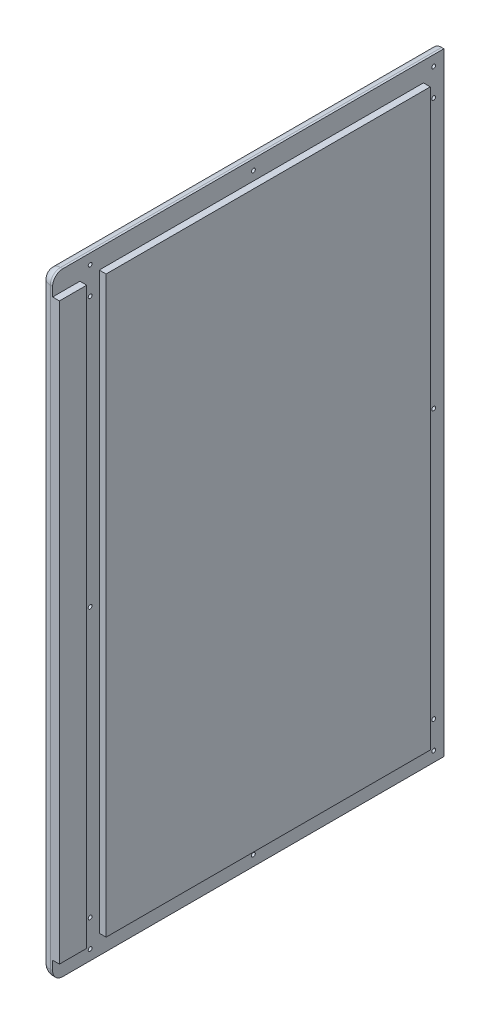
SolidWorks part; units mm, degrees
ref_plane "Front Plane" through (0, 0, 0) normal (0, 0, 1) x (1, 0, 0)
ref_plane "Top Plane" through (0, 0, 0) normal (0, 1, 0) x (1, 0, 0)
ref_plane "Right Plane" through (0, 0, 0) normal (1, 0, 0) x (0, 0, -1)
sketch "Sketch1" plane through (0, 0, 0) normal (1, 0, 0) x (0, 0, -1)
  line L1 (0, 0) -> (376.55, 0)
  line L2 (0, 0) -> (0, 570)
  line L3 (0, 570) -> (376.55, 570)
  line L4 (376.55, 0) -> (376.55, 570)
  dimension "D1" = 376.55
  dimension "D2" = 570
extrude "Boss-Extrude1" add sketch "Sketch1" along normal blind 18
sketch "Sketch5" plane through (18, 0, 0) normal (1, 0, 0) x (0, 0, -1)
  line L0 (0, 570) -> (0, 0) construction
  line L1 (56.1, 563.65) -> (38.1, 563.65)
  line L2 (56.1, 563.65) -> (56.1, 6.35)
  line L3 (56.1, 6.35) -> (38.1, 6.35)
  line L4 (38.1, 563.65) -> (38.1, 6.35)
  line L5 (0, 0) -> (376.55, 0) construction
  line L6 (376.55, 570) -> (0, 570) construction
  dimension "D1" = 18
  dimension "D2" = 38.1
  dimension "D3" = 6.35
  dimension "D4" = 6.35
extrude "Cut-Extrude3" cut sketch "Sketch5" against normal blind 6.35
sketch "Sketch6" plane through (18, 0, 0) normal (1, 0, 0) x (0, 0, -1)
  line L0 (376.55, 0) -> (376.55, 570) construction
  line L1 (376.55, 563.65) -> (363.85, 563.65)
  line L2 (376.55, 563.65) -> (376.55, 6.35)
  line L3 (376.55, 6.35) -> (363.85, 6.35)
  line L4 (363.85, 563.65) -> (363.85, 6.35)
  line L5 (0, 0) -> (376.55, 0) construction
  line L6 (376.55, 570) -> (0, 570) construction
  dimension "D1" = 12.7
  dimension "D2" = 6.35
  dimension "D3" = 6.35
sketch "Sketch7" plane through (18, 0, 0) normal (1, 0, 0) x (0, 0, -1)
  line L0 (376.55, 563.65) -> (376.55, 6.35) construction
  line L1 (0, 0) -> (376.55, 0)
  line L2 (0, 0) -> (0, 18)
  line L3 (0, 18) -> (376.55, 18)
  line L4 (376.55, 0) -> (376.55, 18)
  line L6 (0, 570) -> (376.55, 570)
  line L7 (0, 570) -> (0, 552)
  line L8 (0, 552) -> (376.55, 552)
  line L9 (376.55, 570) -> (376.55, 552)
  dimension "D1" = 18
  dimension "D2" = 18
extrude "Cut-Extrude4" cut sketch "Sketch7" against normal blind 6.35
fillet "Fillet1" radius 9.525 5 edges at (0, 0, -188.275) (0, 285, 0) (0, 570, -188.275) (5.825, 0, 0) (5.825, 570, 0)
sketch "Sketch9" plane through (18, 0, 0) normal (1, 0, 0) x (0, 0, -1)
  line L0 (56.1, 552) -> (376.55, 552) construction
  line L1 (376.55, 18) -> (357.5, 18)
  line L2 (376.55, 18) -> (376.55, 552)
  line L3 (376.55, 552) -> (357.5, 552)
  line L4 (357.5, 18) -> (357.5, 552)
  dimension "D1" = 19.05
extrude "Cut-Extrude6" cut sketch "Sketch9" against normal up to surface (6.35 mm away) up to face at (11.65, 285, -122.1218)
sketch "Sketch10" plane through (18, 0, 0) normal (1, 0, 0) x (0, 0, -1)
  line L0 (376.55, 570) -> (9.525, 570) construction
  line L1 (12.7, 570) -> (0, 570)
  line L2 (12.7, 570) -> (12.7, 0)
  line L3 (12.7, 0) -> (0, 0)
  line L4 (0, 570) -> (0, 0)
  line L5 (0, 552) -> (0, 18) construction
  line L6 (9.525, 0) -> (376.55, 0) construction
  dimension "D1" = 12.7
extrude "Cut-Extrude7" cut sketch "Sketch10" against normal through all
fillet "Fillet2" radius 9.525 5 edges at (10.5875, 570, -12.7) (2.7898, 567.2102, -12.7) (0, 285, -12.7) (10.5875, 0, -12.7) (2.7898, 2.7898, -12.7)
sketch "Sketch11" plane through (11.65, 0, 0) normal (1, 0, 0) x (0, 0, -1)
  line L0 (376.55, 285) -> (-301.8505, 285) construction
  line L1 (376.55, 0) -> (376.55, 570) construction
  line L2 (199.3875, 570) -> (199.3875, -127.0081) construction
  line L3 (376.55, 570) -> (22.225, 570) construction
  line L4 (443.2304, 560.475) -> (-68.0175, 560.475) construction
  line L5 (47.625, 653.0574) -> (47.625, -108.0982) construction
  line L6 (22.225, 0) -> (376.55, 0) construction
  line L7 (509.7607, 9.525) -> (-29.3814, 9.525) construction
  line L8 (38.1, 552) -> (38.1, 18) construction
  line L9 (367.025, -49.5733) -> (367.025, 706.2708) construction
  line L10 (47.625, 34.925) -> (427.6935, 34.925) construction
  line L11 (47.625, 535.075) -> (543.3463, 535.075) construction
  circle A0 centre (47.625, 285) radius 1.7859
  circle A1 centre (47.625, 560.475) radius 1.7859
  circle A2 centre (199.3875, 560.475) radius 1.7859
  circle A3 centre (367.025, 560.475) radius 1.7859
  circle A4 centre (367.025, 285) radius 1.7859
  circle A5 centre (367.025, 9.525) radius 1.7859
  circle A6 centre (199.3875, 9.525) radius 1.7859
  circle A7 centre (47.625, 9.525) radius 1.7859
  circle A8 centre (47.625, 34.925) radius 1.7859
  circle A9 centre (367.025, 34.925) radius 1.7859
  circle A10 centre (47.625, 535.075) radius 1.7859
  circle A11 centre (367.025, 535.075) radius 1.7859
  dimension "D6" = 3.5719
  dimension "D1" = 9.525
  dimension "D2" = 9.525
  dimension "D3" = 9.525
  dimension "D4" = 9.525
  dimension "D5" = 25.4
  dimension "D7" = 25.4
extrude "Cut-Extrude8" cut sketch "Sketch11" against normal through all
